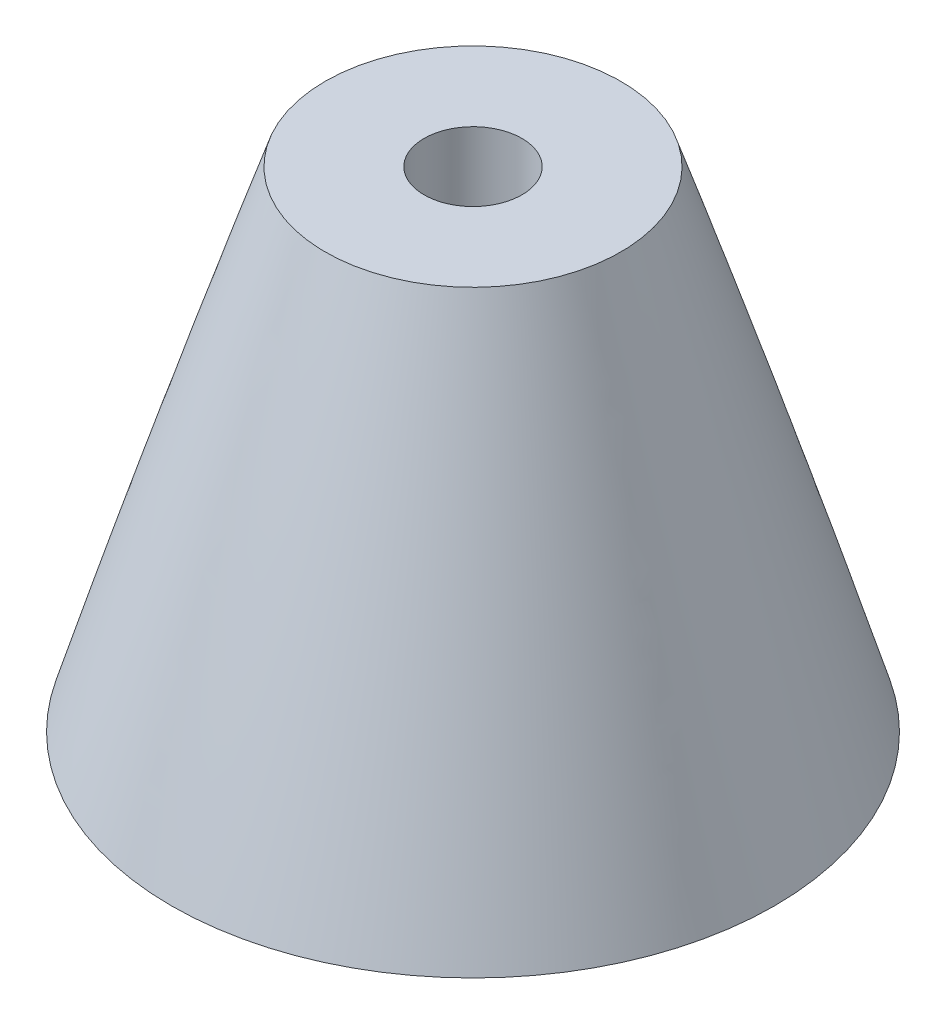
SolidWorks part; units mm, degrees
material "PVB"
ref_plane "Front Plane" through (0, 0, 0) normal (0, 0, 1) x (1, 0, 0)
ref_plane "Top Plane" through (0, 0, 0) normal (0, 1, 0) x (1, 0, 0)
ref_plane "Right Plane" through (0, 0, 0) normal (1, 0, 0) x (0, 0, -1)
sketch "Sketch2" plane through (0, 0, 0) normal (0, 0, 1) x (1, 0, 0)
  line L0 (0, 0) -> (0, 330.2) construction
  line L1 (-76.2, 0) -> (-69.85, 0)
  line L2 (0, 330.2) -> (0, 325.12)
  arc A0 (0, 330.2) -> (-76.2, 0) centre (1014.3906, -77.7824) ccw
  arc A1 (0, 325.12) -> (-69.85, 0) centre (1133.5772, -88.4854) ccw
  dimension "D1" = 330.2
  dimension "D2" = 5.08
  dimension "D3" = 76.2
  dimension "D4" = 6.35
revolve "Revolve1" add sketch "Sketch2" angle 360 about L2
ref_plane "Plane2" through (0, 381, 0) normal (0, 1, 0) x (1, 0, 0)
sketch "Sketch7" plane through (0, 381, 0) normal (0, 1, 0) x (1, 0, 0)
  circle A0 centre (0, 0) radius 317.5
  dimension "D1" = 635
extrude "Cut-Extrude2" cut sketch "Sketch7" against normal blind 88.9
sketch "Sketch9" plane through (0, 0, 0) normal (0, 0, 1) x (1, 0, 0)
  line L0 (-3.81, 292.1) -> (-11.5086, 292.1)
  line L1 (14.5044, 292.1) -> (-14.5044, 292.1) construction
  line L2 (-23.4753, 254) -> (-17.6117, 260.8522)
  line L3 (-17.6117, 260.8522) -> (-10.2467, 285.75)
  line L4 (-10.2467, 285.75) -> (-3.81, 285.75)
  line L5 (-3.81, 285.75) -> (-3.81, 292.1)
  line L6 (0, 0) -> (0, 330.2) construction
  arc A0 (0, 325.12) -> (-69.85, 0) centre (1133.5772, -88.4854) ccw construction
  spline S0 degree 2 poles (-11.5086, 292.1) (-17.8068, 273.1501) (-23.4753, 254) knots 0 0 0 1 1 1
  point P14 (-17.6117, 260.8522)
  dimension "D1" = 38.1
  dimension "D2" = 6.35
  dimension "D3" = 3.81
revolve "Revolve2" add sketch "Sketch9" angle 360 about L0
sketch "Sketch10" plane through (0, 0, 0) normal (0, -1, 0) x (1, 0, 0)
  circle A0 centre (0, 0) radius 85.7722
extrude "Cut-Extrude3" cut sketch "Sketch10" against normal blind 254
sketch "Sketch11" plane through (0, 0, 0) normal (0, 0, 1) x (1, 0, 0)
  line L0 (0, 292.1) -> (0, 251.2136) construction
  line L1 (14.5044, 292.1) -> (-14.5044, 292.1) construction
  line L2 (-11.5086, 292.1) -> (-17.2183, 292.1)
  line L3 (-17.2183, 292.1) -> (-28.8776, 252.5819)
  line L4 (-28.8776, 252.5819) -> (-23.4753, 254)
  arc A0 (-11.5086, 292.1) -> (-23.4753, 254) centre (1133.5921, -88.4901) ccw construction
  spline S0 degree 2 poles (-23.4753, 254) (-17.8072, 273.1489) (-11.5086, 292.1) knots 0 0 0 1 1 1
revolve "Cut-Revolve1" cut sketch "Sketch11" angle 360 about L0
